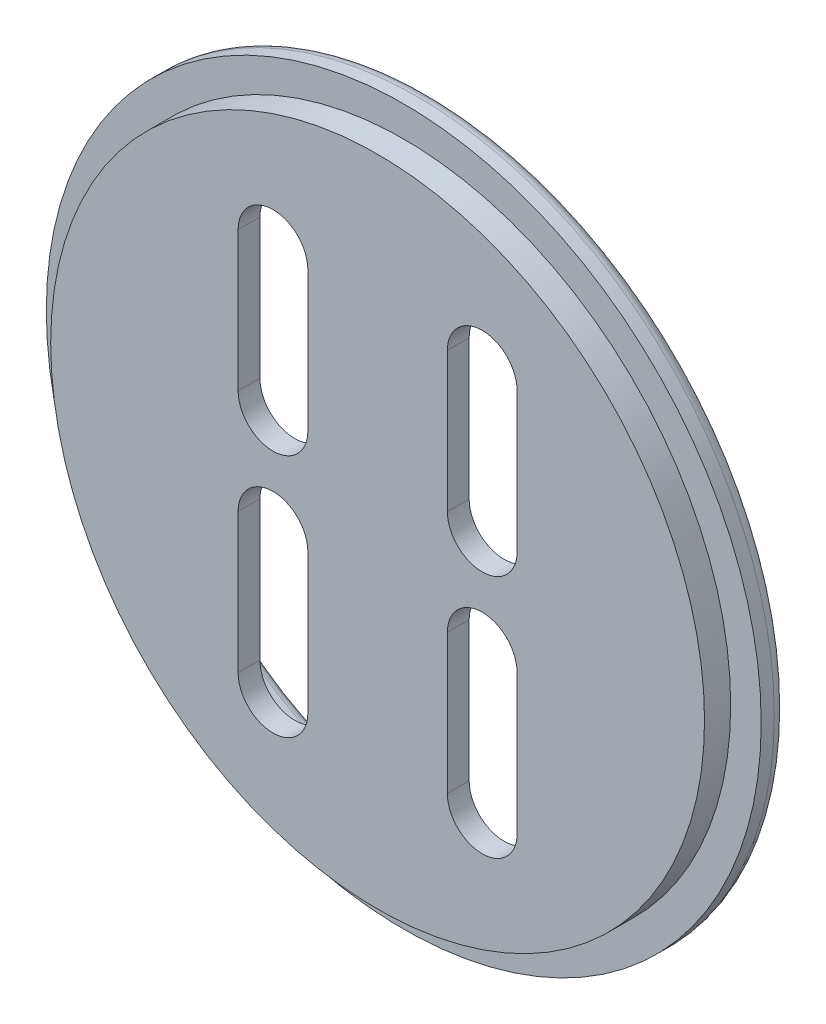
SolidWorks part; units mm, degrees
ref_plane "Front Plane" through (0, 0, 0) normal (0, 0, 1) x (1, 0, 0)
ref_plane "Top Plane" through (0, 0, 0) normal (0, 1, 0) x (1, 0, 0)
ref_plane "Right Plane" through (0, 0, 0) normal (1, 0, 0) x (0, 0, -1)
sketch "Sketch1" plane through (0, 0, 0) normal (0, 0, 1) x (1, 0, 0)
  circle A0 centre (0, 0) radius 41
extrude "Boss-Extrude1" add sketch "Sketch1" along normal blind 3 contours A0
sketch "Sketch2" plane through (0, 0, 3) normal (0, 0, 1) x (1, 0, 0)
  circle A0 centre (0, 0) radius 37.5
extrude "Boss-Extrude4" add sketch "Sketch2" along normal blind 3
sketch "Sketch5" plane through (0, 0, 0) normal (0, 0, -1) x (-1, 0, 0)
  circle A0 centre (0, 0) radius 31.5
extrude "Cut-Extrude3" cut sketch "Sketch5" against normal blind 3.5
sketch "Sketch6" plane through (0, 0, 3.5) normal (0, 0, -1) x (-1, 0, 0)
  line L5 (-12, 6) -> (-12, 22) construction
  line L6 (-16, 6) -> (-16, 22)
  line L7 (-8, 6) -> (-8, 22)
  line L8 (12, 6) -> (12, 22) construction
  line L9 (16, 6) -> (16, 22)
  line L10 (8, 6) -> (8, 22)
  line L11 (12, -6) -> (12, -22) construction
  line L12 (16, -6) -> (16, -22)
  line L13 (8, -6) -> (8, -22)
  line L14 (-12, -6) -> (-12, -22) construction
  line L15 (-16, -6) -> (-16, -22)
  line L16 (-8, -6) -> (-8, -22)
  arc A0 (-16, 6) -> (-8, 6) centre (-12, 6) ccw
  arc A1 (-8, 22) -> (-16, 22) centre (-12, 22) ccw
  arc A2 (16, 6) -> (8, 6) centre (12, 6) cw
  arc A3 (8, 22) -> (16, 22) centre (12, 22) cw
  arc A4 (16, -6) -> (8, -6) centre (12, -6) ccw
  arc A5 (8, -22) -> (16, -22) centre (12, -22) ccw
  arc A6 (-16, -6) -> (-8, -6) centre (-12, -6) cw
  arc A7 (-8, -22) -> (-16, -22) centre (-12, -22) cw
  point P3 (-12, 14)
  point P16 (12, 14)
  point P23 (12, -14)
  point P30 (-12, -14)
extrude "Cut-Extrude6" cut sketch "Sketch6" against normal blind 3
fillet "Fillet3" radius 1 1 edges at (-31.5, 0, 0)
fillet "Fillet4" radius 1.5 1 edges at (41, 0, 0)
fillet "Fillet5" radius 1 1 edges at (-31.5, 0, 3.5)
